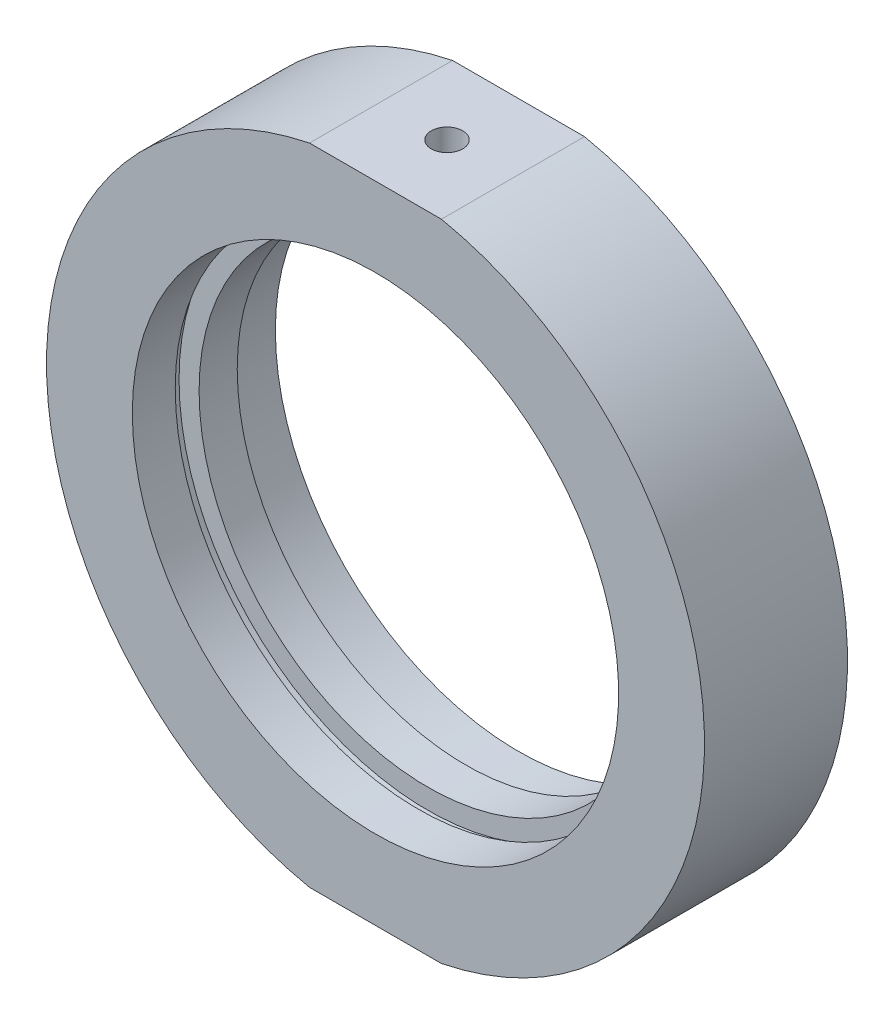
SolidWorks part; units mm, degrees
ref_plane "前视基准面" through (0, 0, 0) normal (0, 0, 1) x (1, 0, 0)
ref_plane "上视基准面" through (0, 0, 0) normal (0, 1, 0) x (1, 0, 0)
ref_plane "右视基准面" through (0, 0, 0) normal (1, 0, 0) x (0, 0, -1)
sketch "草图1" plane through (0, 0, 0) normal (0, 1, 0) x (1, 0, 0)
  line L0 (0, 31.9391) -> (0, -26.491) construction
  line L1 (34.5, 7.5) -> (34.5, -7.5)
  line L2 (25.5, 2) -> (26.1, 2)
  line L3 (26.1, 2) -> (26.1, 3)
  line L4 (26.1, 3) -> (25.5, 3)
  line L5 (25.5, -2) -> (26.1, -2)
  line L6 (34.5, -7.5) -> (25.5, -7.5)
  line L7 (25.5, -7.5) -> (25.5, -3)
  line L8 (25.5, -2) -> (24, -2)
  line L9 (24, -2) -> (24, 2)
  line L10 (24, 2) -> (25.5, 2)
  line L11 (25.5, 3) -> (25.5, 7.5)
  line L12 (25.5, 7.5) -> (34.5, 7.5)
  line L13 (26.1, -2) -> (26.1, -3)
  line L14 (26.1, -3) -> (25.5, -3)
  line L17 (19.05, 0) -> (-5.0345, 0) construction
  point P6 (24, 0)
  dimension "D2" = 24
  dimension "D3" = 25.5
  dimension "D4" = 25.5
  dimension "D5" = 15
  dimension "D6" = 5.5
  dimension "D7" = 5.5
  dimension "D8" = 26.1
  dimension "D9" = 34.5
  dimension "D10" = 26.1
  dimension "D11" = 1
  dimension "D12" = 1
  dimension "D13" = 7.5
  dimension "D18" = 0
revolve "旋转1" add sketch "草图1" angle 360 about L0
cosmetic thread "装饰螺纹线1" parameters "D2"=52
cosmetic thread "装饰螺纹线2" parameters "D2"=52
sketch "草图2" plane through (0, 0, 7.5) normal (0, 0, 1) x (1, 0, 0)
  line L0 (0, 0) -> (43.1523, 0) construction
  line L1 (-33.152, 43.0489) -> (30.8698, 43.0489)
  line L2 (-33.152, 43.0489) -> (-33.152, 33.8)
  line L3 (-33.152, 33.8) -> (30.8698, 33.8)
  line L4 (30.8698, 43.0489) -> (30.8698, 33.8)
  line L5 (30.8698, -43.0489) -> (30.8698, -33.8)
  line L6 (-33.152, -33.8) -> (30.8698, -33.8)
  line L7 (-33.152, -43.0489) -> (-33.152, -33.8)
  line L8 (-33.152, -43.0489) -> (30.8698, -43.0489)
  dimension "D1" = 33.8
extrude "切除-拉伸1" cut sketch "草图2" against normal blind 49
sketch "草图10" plane through (0, 0, 0) normal (0, 0, 1) x (1, 0, 0)
  line L0 (0, 33.8) -> (0, -33.8)
  line L1 (-6.9145, 33.8) -> (6.9145, 33.8) construction
  line L2 (-6.9145, -33.8) -> (6.9145, -33.8) construction
  line L3 (0, 0) -> (-29.8779, 17.25)
  line L4 (0, 0) -> (29.8779, 17.25)
  arc A2 (6.9145, -33.8) -> (6.9145, 33.8) centre (0, 0) ccw construction
  arc A3 (-6.9145, 33.8) -> (-6.9145, -33.8) centre (0, 0) ccw construction
  arc A4 (29.8779, 17.25) -> (6.9145, 33.8) centre (0, 0) ccw
  arc A5 (-6.9145, 33.8) -> (-29.8779, 17.25) centre (0, 0) ccw
  dimension "D1" = 60
  dimension "D2" = 60
hole_wizard "M4 螺纹孔2" positions "草图15" profile "草图16" tap size "M4" standard "ISO"
sketch "草图15" plane through (0, 33.8, 0) normal (0, 1, 0) x (1, 0, 0)
  point P0 (0, 0)
sketch "草图16" plane through (0, 33.8, 0) normal (1, 0, 0) x (0, 0, 1)
  line L0 (0, 0) -> (0, 6.4914)
  line L1 (0, 6.4914) -> (1.65, 5.5)
  line L2 (1.65, 5.5) -> (1.65, 0)
  line L5 (1.65, 0) -> (0, 0)
  line L10 (0, 6.4914) -> (-1.65, 5.5) construction
  line L11 (0, -6.35) -> (0, 107.95) construction
  dimension "螺纹孔钻头直径" = 3.3
  dimension "螺纹孔钻头深度" = 5.5
  dimension "导头角度" = 118
cosmetic thread "孔螺蚊线6" parameters "D1"=5.5, "D2"=4
hole_wizard "M6 螺纹孔2" positions "草图17" profile "草图18" tap size "M6" standard "ISO"
sketch "草图17" plane through (0, -33.8, 0) normal (0, -1, 0) x (-1, 0, 0)
  point P0 (0, 0)
sketch "草图18" plane through (0, -33.8, 0) normal (1, 0, 0) x (0, 0, -1)
  line L0 (0, 0) -> (0, 7.0022)
  line L1 (0, 7.0022) -> (2.5, 5.5)
  line L2 (2.5, 5.5) -> (2.5, 0)
  line L5 (2.5, 0) -> (0, 0)
  line L10 (0, 7.0022) -> (-2.5, 5.5) construction
  line L11 (0, -6.35) -> (0, 107.95) construction
  dimension "螺纹孔钻头直径" = 5
  dimension "螺纹孔钻头深度" = 5.5
  dimension "导头角度" = 118
cosmetic thread "孔螺蚊线7" parameters "D1"=5.5, "D2"=6
